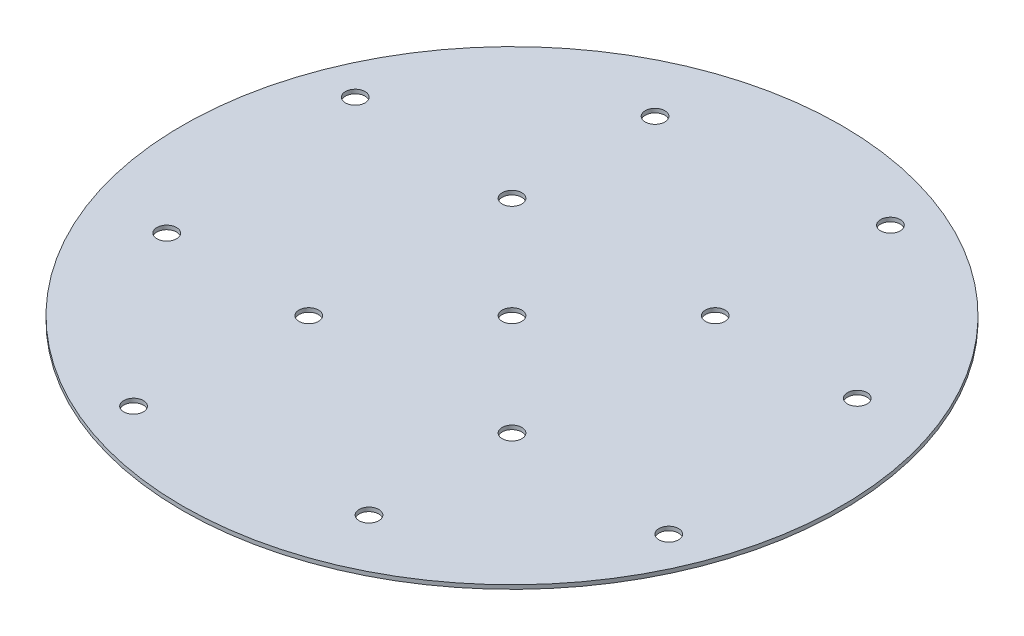
SolidWorks part; units mm, degrees
material "6061-T6 (SS)"
ref_plane "Front Plane" through (0, 0, 0) normal (0, 0, 1) x (1, 0, 0)
ref_plane "Top Plane" through (0, 0, 0) normal (0, 1, 0) x (1, 0, 0)
ref_plane "Right Plane" through (0, 0, 0) normal (1, 0, 0) x (0, 0, -1)
sketch "Sketch2" plane through (0, 0, 0) normal (1, 0, 0) x (0, 0, -1)
  line L0 (0, 0) -> (-82.55, 0)
  line L1 (-82.55, 0) -> (-82.55, 1)
  line L2 (-82.55, 1) -> (0, 1)
  line L5 (0, 1) -> (0, 0)
  dimension "D1" = 82.55
  dimension "D2" = 1
ref_axis "Axis1" through (0, -0.05, 0) along (0, 1, 0)
revolve "Revolve1" add sketch "Sketch2" angle 360 about axis through (0, -0.05, 0) along (0, 1, 0)
hole_wizard "#10 (0.1935) Diameter Hole1" positions "Sketch6" profile "Sketch7" hole size "#10" standard "ANSI Inch" end condition through all
sketch "Sketch6" plane through (0, 1, 0) normal (0, 1, 0) x (1, 0, 0)
  line L0 (0, 0) -> (-53.438, 129.0108) construction
  line L2 (0, 0) -> (0, 109.0908) construction
  line L3 (0, 0) -> (-76.2663, 31.5905) construction
  line L4 (0, 0) -> (-47.7784, 47.7784) construction
  circle A0 centre (0, 0) radius 82.55 construction
  point P0 (-25.3336, 61.1608)
  point P11 (264.7437, 73.7878)
  point P20 (-67.0275, 27.7637)
  point P22 (-25.4558, 25.4558)
  dimension "D1" = 22.5
  dimension "D2" = 66.2
  dimension "D3" = 72.55
  dimension "D4" = 45
  dimension "D6" = 22.5
  dimension "D5" = 36
sketch "Sketch7" plane through (-25.3336, 1, -61.1608) normal (1, 0, 0) x (0, 0, 1)
  line L0 (0, 0) -> (0, 1)
  line L1 (0, 1) -> (2.4574, 1)
  line L2 (2.4574, 1) -> (2.4574, 0)
  line L5 (2.4574, 0) -> (0, 0)
  line L11 (0, -6.35) -> (0, 107.95) construction
  dimension "Thru Hole Dia." = 4.9149
  dimension "Thru Hole Depth" = 1
pattern_circular "CirPattern3" count 4 over 360 about axis through (0, 0, 0) along (0, 1, 0) of "#10 (0.1935) Diameter Hole1"
hole_wizard "#10 (0.1935) Diameter Hole2" positions "Sketch8" profile "Sketch9" hole size "#10" standard "ANSI Inch" end condition through all
sketch "Sketch8" plane through (0, 1, 0) normal (0, 1, 0) x (1, 0, 0)
  line L0 (0, 0) -> (106.3094, -1.7118) construction
  point P7 (0, 0)
sketch "Sketch9" plane through (0, 1, 0) normal (1, 0, 0) x (0, 0, 1)
  line L0 (0, 0) -> (0, 1)
  line L1 (0, 1) -> (2.4574, 1)
  line L2 (2.4574, 1) -> (2.4574, 0)
  line L5 (2.4574, 0) -> (0, 0)
  line L11 (0, -6.35) -> (0, 107.95) construction
  dimension "Thru Hole Dia." = 4.9149
  dimension "Thru Hole Depth" = 1
equation "\"TubeDiameter\"= 6.500in"
equation "\"D1@Sketch2\"=\"TubeDiameter\"/2"
equation "\"D2@Sketch6\"=66.2"
equation "\"D3@Sketch6\"=\"TubeDiameter\"/2-10mm"
